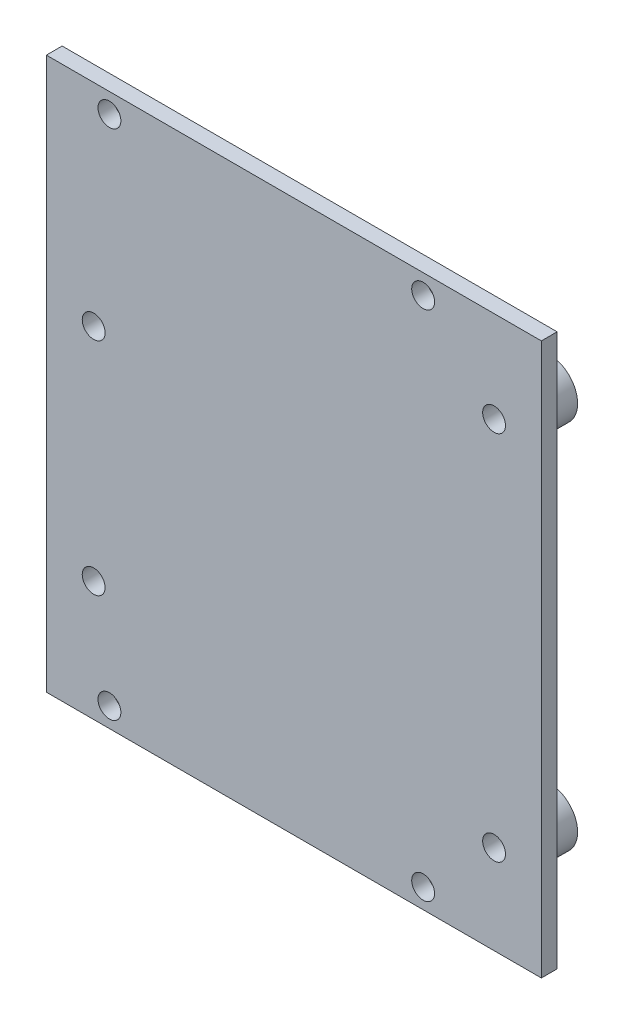
SolidWorks part; units mm, degrees
ref_plane "Front Plane" through (0, 0, 0) normal (0, 0, 1) x (1, 0, 0)
ref_plane "Top Plane" through (0, 0, 0) normal (0, 1, 0) x (1, 0, 0)
ref_plane "Right Plane" through (0, 0, 0) normal (1, 0, 0) x (0, 0, -1)
sketch "Sketch1" plane through (0, 0, 0) normal (0, 0, 1) x (1, 0, 0)
  circle A0 centre (17.8, 23.54) radius 1.6 construction
  circle A1 centre (-33, 8.34) radius 1.6 construction
  circle A2 centre (17.8, -23.54) radius 1.6 construction
  circle A3 centre (-33, -19.66) radius 1.6 construction
  circle A4 centre (17.8, 23.54) radius 1.6
  circle A5 centre (-33, 8.34) radius 1.6
  circle A6 centre (17.8, -23.54) radius 1.6
  circle A7 centre (-33, -19.66) radius 1.6
  circle A8 centre (17.8, 23.54) radius 3.6
  circle A9 centre (-33, 8.34) radius 3.6
  circle A10 centre (17.8, -23.54) radius 3.6
  circle A11 centre (-33, -19.66) radius 3.6
  dimension "D1" = 2
extrude "Boss-Extrude1" add sketch "Sketch1" along normal blind 5 contours A7 | A11 A7 | A9 | A10 | A8
sketch "Sketch2" plane through (0, 0, 5) normal (0, 0, 1) x (1, 0, 0)
  line L0 (-34.1225, -34.87) -> (-46.9687, -34.87) construction
  line L1 (23.8, -34.87) -> (-39, -34.87)
  line L2 (23.8, -34.87) -> (23.8, 35.13)
  line L3 (23.8, 35.13) -> (-39, 35.13)
  line L4 (-39, -34.87) -> (-39, 35.13)
  line L5 (-46.9687, 35.13) -> (-34.1225, 35.13) construction
  circle A0 centre (-33, -19.66) radius 3.6 construction
  circle A1 centre (17.8, -23.54) radius 3.6 construction
  dimension "D2" = 6
  dimension "D1" = 6
extrude "Boss-Extrude2" add sketch "Sketch2" along normal blind 2
sketch "Sketch3" plane through (0, 0, 7) normal (0, 0, 1) x (1, 0, 0)
  circle A1 centre (8.8, 32.63) radius 4
  circle A2 centre (8.8, 32.63) radius 4
  circle A3 centre (-31, 32.63) radius 4
  circle A4 centre (-31, 32.63) radius 4
  circle A5 centre (-31, -32.37) radius 4
  circle A6 centre (-31, -32.37) radius 4
  circle A7 centre (8.8, -32.37) radius 4
  circle A8 centre (8.8, -32.37) radius 4
  dimension "D1" = 0
  dimension "D2" = 0
  dimension "D3" = 0
  dimension "D4" = 0
hole_wizard "Ø1.0mm Dowel Hole2" positions "3DSketch1" profile "Sketch4" hole size "Ø1.0" standard "ANSI Metric"
sketch3d "3DSketch1"
  point P0 (8.8, -32.37, 7)
  point P3 (-31, -32.37, 7)
  point P6 (-31, 32.63, 7)
  point P17 (8.8, 32.63, 7)
sketch "Sketch4" plane through (8.8, -32.37, 7) normal (1, 0, 0) x (0, -1, 0)
  line L0 (0, 0) -> (0, 10)
  line L1 (0, 10) -> (1.45, 9.1288)
  line L2 (1.45, 9.1288) -> (1.45, 0)
  line L5 (1.45, 0) -> (0, 0)
  line L10 (0, 10) -> (-1.45, 9.1288) construction
  line L11 (0, -6.35) -> (0, 107.95) construction
  dimension "Hole Dia." = 2.9
  dimension "Hole Depth" = 10
  dimension "Drill Angle" = 118
hole_wizard "Ø1.0mm Dowel Hole3" positions "3DSketch2" profile "Sketch5" hole size "Ø1.0" standard "ANSI Metric"
sketch3d "3DSketch2"
  line L0 (17.8, 23.54, 5) -> (17.8, 23.54, 0) construction
  line L1 (-33, 8.34, 5) -> (-33, 8.34, 0) construction
  line L2 (-33, -19.66, 5) -> (-33, -19.66, 0) construction
  line L3 (17.8, -23.54, 5) -> (17.8, -23.54, 0) construction
  point P0 (17.8, 23.54, 0)
  point P4 (-33, 8.34, 0)
  point P8 (-33, -19.66, 0)
  point P12 (17.8, -23.54, 0)
sketch "Sketch5" plane through (17.8, 23.54, 0) normal (1, 0, 0) x (0, 1, 0)
  line L0 (0, 0) -> (0, 10)
  line L1 (0, 10) -> (1.45, 9.1288)
  line L2 (1.45, 9.1288) -> (1.45, 0)
  line L5 (1.45, 0) -> (0, 0)
  line L10 (0, 10) -> (-1.45, 9.1288) construction
  line L11 (0, -6.35) -> (0, 107.95) construction
  dimension "Hole Dia." = 2.9
  dimension "Hole Depth" = 10
  dimension "Drill Angle" = 118
